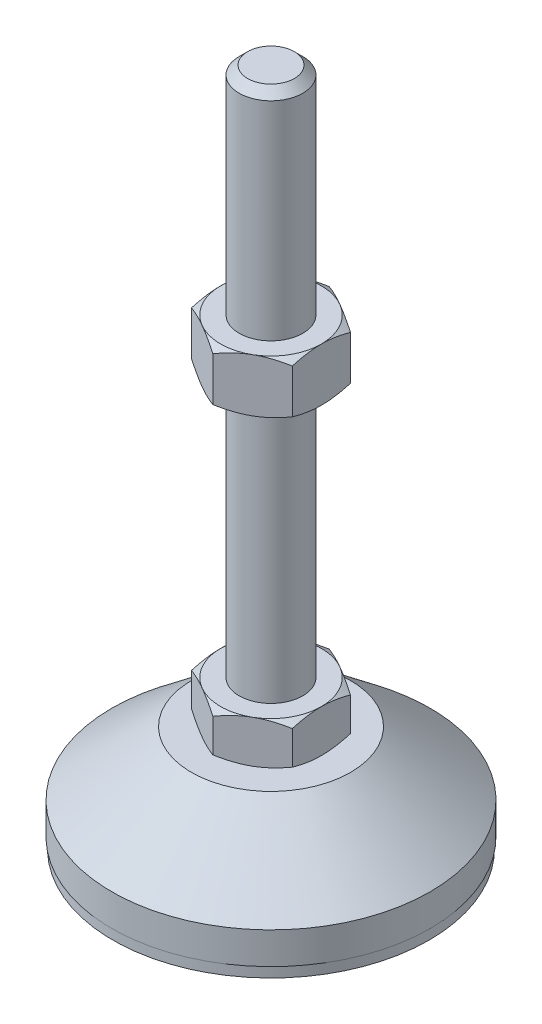
SolidWorks part; units mm, degrees
ref_plane "Спереди" through (0, 0, 0) normal (0, 0, 1) x (1, 0, 0)
ref_plane "Сверху" through (0, 0, 0) normal (0, 1, 0) x (1, 0, 0)
ref_plane "Справа" through (0, 0, 0) normal (1, 0, 0) x (0, 0, -1)
sketch "Эскиз1" plane through (0, 0, 0) normal (0, 0, 1) x (1, 0, 0)
  line L0 (0, 0) -> (-29.8, 0)
  line L1 (-29.8, 0) -> (-29.8, 2)
  line L2 (-29.8, 2) -> (-30, 2)
  line L3 (-30, 2) -> (-30, 8)
  line L4 (-30, 8) -> (-15, 20)
  line L5 (-15, 20) -> (-6, 20)
  line L12 (-6, 28) -> (-6, 126.4)
  line L13 (-6, 126.4) -> (-4.4, 128)
  line L14 (-4.4, 128) -> (0, 128)
  line L15 (0, 128) -> (0, 0) construction
  line L16 (-6, 20) -> (0, 20) construction
  line L17 (0, 0) -> (0, 128)
  line L18 (0, 0) -> (0, -7.9595) construction
  line L19 (-6, 28) -> (-6, 20)
  point P8 (-6, 77.2)
  point P23 (-10.5, 20)
  dimension "D1" = 12
  dimension "D2" = 20
  dimension "D3" = 8
  dimension "D4" = 60
  dimension "D5" = 6
  dimension "D6" = 1.6
  dimension "D7" = 45
  dimension "D8" = 30
  dimension "D9" = 2
  dimension "D10" = 100
  dimension "D11" = 6
  dimension "D12" = 0.2
revolve "Повернуть1" add sketch "Эскиз1" angle 360 about L17
sketch "Эскиз2" plane through (0, 20, 0) normal (0, 1, 0) x (1, 0, 0)
  line L1 (0, 10.9697) -> (-9.5, 5.4848)
  line L2 (-9.5, 5.4848) -> (-9.5, -5.4848)
  line L3 (-9.5, -5.4848) -> (0, -10.9697)
  line L4 (0, -10.9697) -> (9.5, -5.4848)
  line L5 (9.5, -5.4848) -> (9.5, 5.4848)
  line L6 (9.5, 5.4848) -> (0, 10.9697)
  circle A0 centre (0, 0) radius 9.5 construction
  dimension "D1" = 19
extrude "Бобышка-Вытянуть1" add sketch "Эскиз2" along normal up to vertex (8 mm away) up to point (-6, 28, 0)
ref_plane "Плоскость1" through (0, 77.2, 0) normal (0, 1, 0) x (1, 0, 0)
sketch "Эскиз3" plane through (0, 77.2, 0) normal (0, 1, 0) x (1, 0, 0)
  line L6 (9.5, 5.4848) -> (0, 10.9697)
  line L7 (0, 10.9697) -> (-9.5, 5.4848)
  line L8 (-9.5, 5.4848) -> (-9.5, -5.4848)
  line L9 (-9.5, -5.4848) -> (0, -10.9697)
  line L10 (0, -10.9697) -> (9.5, -5.4848)
  line L11 (9.5, -5.4848) -> (9.5, 5.4848)
  line L12 (9.5, 5.4848) -> (0, 10.9697)
  line L13 (0, 10.9697) -> (-9.5, 5.4848)
  line L14 (-9.5, 5.4848) -> (-9.5, -5.4848)
  line L15 (-9.5, -5.4848) -> (0, -10.9697)
  line L16 (0, -10.9697) -> (9.5, -5.4848)
  line L17 (9.5, -5.4848) -> (9.5, 5.4848)
  dimension "D1" = 0
extrude "Бобышка-Вытянуть2" add sketch "Эскиз3" along normal blind 10
sketch "Эскиз4" plane through (0, 0, 0) normal (0, 0, 1) x (1, 0, 0)
  line L0 (-9.5, 87.2) -> (-18.1603, 82.2)
  line L1 (-18.1603, 82.2) -> (-18.1603, 87.2)
  line L2 (-18.1603, 87.2) -> (-9.5, 87.2)
  line L3 (-18.1603, 82.2) -> (-9.5, 77.2)
  line L4 (50, 77.2) -> (-50, 77.2) construction
  line L5 (-9.5, 77.2) -> (-18.1603, 77.2)
  line L6 (-18.1603, 77.2) -> (-18.1603, 82.2)
  line L7 (-9.5, 87.2) -> (-9.5, 77.2) construction
  line L8 (-9.5, 28) -> (-16.4282, 28)
  line L9 (-16.4282, 28) -> (-16.4282, 24)
  line L10 (-16.4282, 24) -> (-9.5, 28)
  line L11 (-9.5, 20) -> (-16.4282, 24)
  line L12 (-16.4282, 24) -> (-16.4282, 20)
  line L13 (-16.4282, 20) -> (-9.5, 20)
  line L14 (0, 128) -> (0, 96.3793) construction
  dimension "D1" = 30
  dimension "D2" = 30
revolve "Вырез-Повернуть2" cut sketch "Эскиз4" angle 360 about L14
